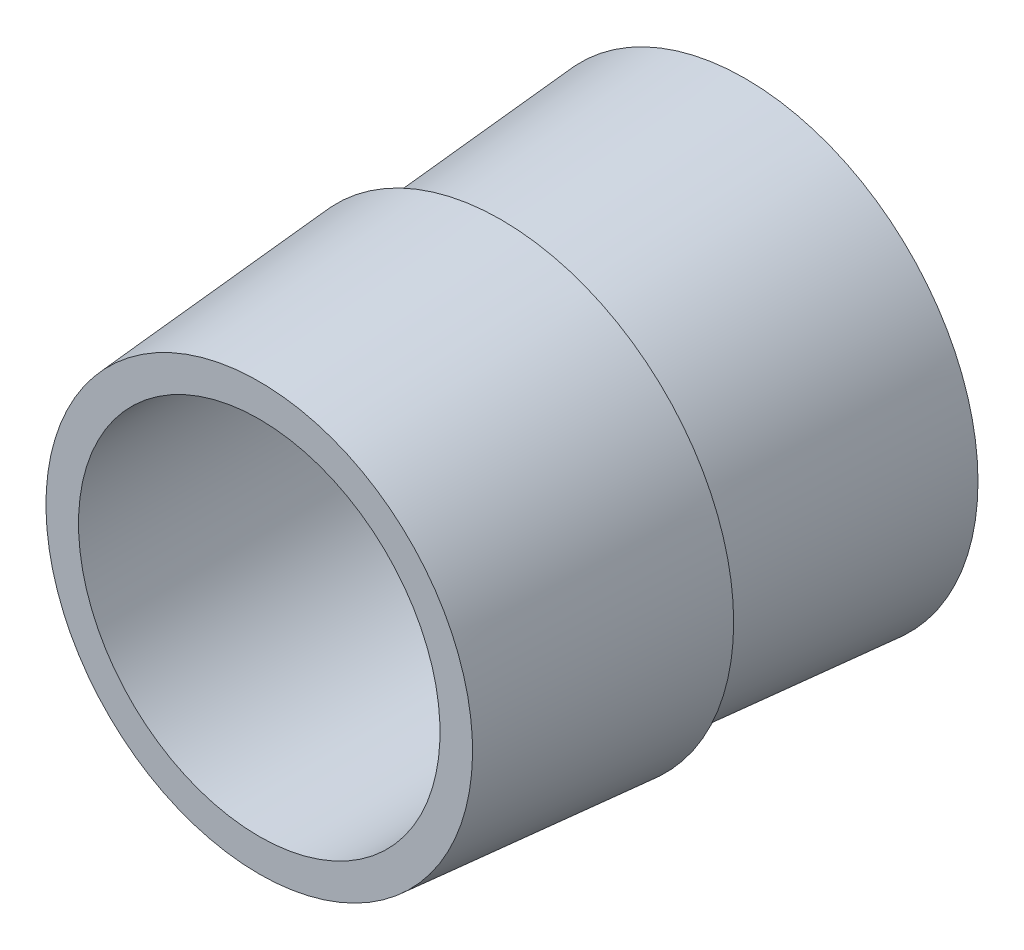
SolidWorks part; units mm, degrees
ref_plane "Front Plane" through (0, 0, 0) normal (0, 0, 1) x (1, 0, 0)
ref_plane "Top Plane" through (0, 0, 0) normal (0, 1, 0) x (1, 0, 0)
ref_plane "Right Plane" through (0, 0, 0) normal (1, 0, 0) x (0, 0, -1)
sketch "Sketch2" plane through (0, 0, 0) normal (1, 0, 0) x (0, 0, -1)
  line L0 (-0.5417, -1.2698) -> (6.8523, -1.2698)
  line L4 (-4.1476, 0.981) -> (-0.5417, 1.2671) construction
  line L5 (-0.5417, 1.2671) -> (-0.5417, 1.975)
  line L7 (3.1381, 1.2671) -> (3.1381, 1.975)
  line L9 (6.8523, 1.2698) -> (6.8523, -1.2698)
  line L10 (-4.1476, 0.981) -> (-4.2216, 0.9751)
  line L13 (-4.2216, 0.9751) -> (-4.2216, -1.2698) construction
  line L14 (-0.5417, 0.975) -> (-0.5417, -1.2698)
  line L15 (-0.5417, -1.2698) -> (-4.2216, -1.2698) construction
  line L16 (6.8523, 1.2698) -> (3.1381, 0.975) construction
  line L17 (3.1381, 1.2671) -> (-0.5417, 0.975) construction
  line L18 (3.1381, 1.2671) -> (3.1381, 2.2671)
  line L19 (3.1381, 2.2671) -> (-0.5417, 1.975)
  line L21 (6.8523, 1.2698) -> (6.8523, 2.2698)
  line L22 (6.8523, 2.2698) -> (3.1381, 1.975)
  line L23 (3.1381, 1.975) -> (3.1381, 0.975) construction
  line L24 (-0.5417, 1.2671) -> (-0.5417, 1.7692) construction
  line L25 (-0.5417, 1.2671) -> (-0.5417, 0.975)
  dimension "D1" = 1
  dimension "D2" = 1
revolve "Revolve2" add sketch "Sketch2" angle 360 about L0
sketch "Sketch7" plane through (0, 0, -6.8523) normal (0, 0, -1) x (-1, 0, 0)
  line L0 (0, 2.2698) -> (0, -4.8095) construction
  circle A0 centre (0, -1.2698) radius 3.5397 construction
  circle A1 centre (0, -1.2698) radius 2.75
  dimension "D1" = 5.5
extrude "Cut-Extrude3" cut sketch "Sketch7" against normal through all
